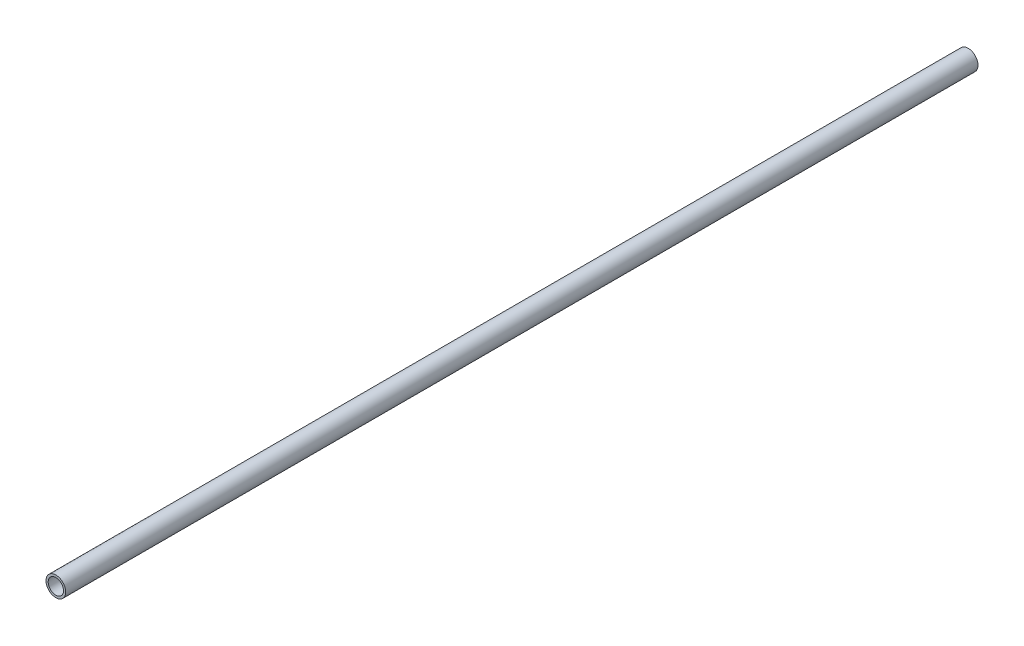
SolidWorks part; units mm, degrees
material "Galvanized Steel"
ref_plane "Front" through (0, 0, 0) normal (0, 0, 1) x (1, 0, 0)
ref_plane "Top" through (0, 0, 0) normal (0, 1, 0) x (1, 0, 0)
ref_plane "Right" through (0, 0, 0) normal (1, 0, 0) x (0, 0, -1)
sketch "Sketch1" plane through (0, 0, 0) normal (0, 0, 1) x (1, 0, 0)
  circle A0 centre (-7.3192, 4.997) radius 13.716
  dimension "D1" = 27.432
extrude "Boss-Extrude1" add sketch "Sketch1" along normal blind 1270
sketch "Sketch2" plane through (0, 0, 0) normal (0, 0, -1) x (-1, 0, 0)
  circle A0 centre (7.3192, 4.997) radius 10.668
  dimension "D1" = 21.336
extrude "Cut-Extrude1" cut sketch "Sketch2" against normal through all
